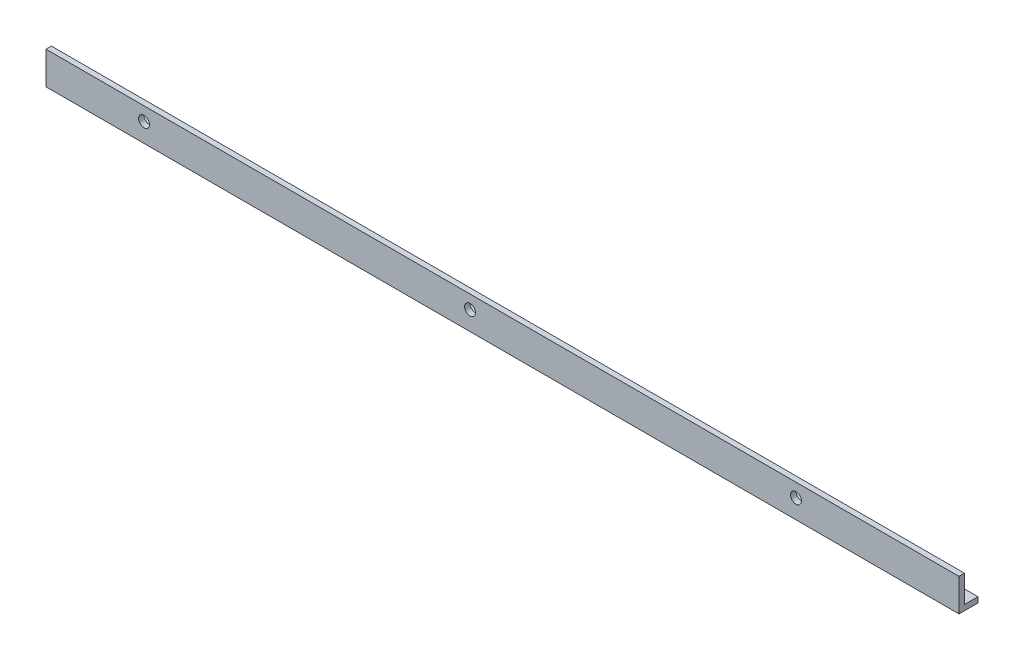
SolidWorks part; units mm, degrees
other "Markup1"
sketch "Sketch9" plane through (-9.88, -1.52, -2.5) normal (-1, 0, 0) x (0, 0, 1)
ref_plane "Alzado" through (0, 0, 0) normal (0, 0, 1) x (1, 0, 0)
ref_plane "Planta" through (0, 0, 0) normal (0, 1, 0) x (1, 0, 0)
ref_plane "Vista lateral" through (0, 0, 0) normal (1, 0, 0) x (0, 0, -1)
sketch "Sketch1" plane through (0, 0, 0) normal (0, 0, 1) x (1, 0, 0)
  line L1 (-14.6, 8.48) -> (50.12, 8.48)
  line L2 (-14.6, 8.48) -> (-14.6, -1.52)
  line L3 (-14.6, -1.52) -> (50.12, -1.52)
  line L4 (50.12, 8.48) -> (50.12, -1.52)
  dimension "D1" = 10
extrude "Boss-Extrude1" add sketch "Sketch1" along normal blind 1
sketch "Sketch2" plane through (0, 0, 0) normal (0, 0, -1) x (-1, 0, 0)
  line L0 (14.6, 8.48) -> (14.6, -1.52) construction
  line L1 (-50.12, -1.52) -> (14.6, -1.52)
  line L2 (-50.12, -1.52) -> (-50.12, -0.52)
  line L3 (-50.12, -0.52) -> (14.6, -0.52)
  line L4 (14.6, -1.52) -> (14.6, -0.52)
  dimension "D1" = 1
extrude "Boss-Extrude2" add sketch "Sketch2" along normal blind 5
sketch "Sketch3" plane through (50.12, 0, 0) normal (1, 0, 0) x (0, 0, -1)
  line L0 (-1, 8.48) -> (0, 8.48)
  line L1 (0, 8.48) -> (0, -0.52)
  line L2 (0, -0.52) -> (5, -0.52)
  line L3 (5, -0.52) -> (5, -1.52)
  line L4 (-1, -1.52) -> (5, -1.52) construction
  line L5 (5, -1.52) -> (-1, -1.52)
  line L6 (-1, -1.52) -> (-1, 8.48)
extrude "Boss-Extrude3" add sketch "Sketch3" along normal blind 60
sketch "Sketch4" plane through (110.12, 0, 0) normal (1, 0, 0) x (0, 0, -1)
  line L0 (0, -0.52) -> (0, 8.48) construction
  line L1 (-1, 8.48) -> (0, 8.48)
  line L2 (-1, 8.48) -> (-1, 3.48)
  line L3 (-1, 3.48) -> (0, 3.48)
  line L4 (0, 8.48) -> (0, 3.48)
  dimension "D1" = 5
extrude "Cut-Extrude1" cut sketch "Sketch4" against normal through all
sketch "Sketch5" plane through (0, 3.48, 0) normal (0, 1, 0) x (1, 0, 0)
  line L0 (110.12, -1) -> (-9.88, -1) construction
  line L1 (-14.6, -1) -> (110.12, -1) construction
  line L3 (-9.88, -1) -> (-14.6, -1)
  line L4 (-9.88, -1) -> (-9.88, 5)
  line L5 (-9.88, 5) -> (-14.6, 5)
  line L6 (-14.6, -1) -> (-14.6, 5)
  dimension "D1" = 120
extrude "Cut-Extrude2" cut sketch "Sketch5" against normal through all
sketch "Sketch6" plane through (0, 3.48, 0) normal (0, 1, 0) x (1, 0, 0)
  line L1 (-9.88, 0) -> (110.12, 0)
  line L2 (-9.88, 0) -> (-9.88, -1)
  line L3 (-9.88, -1) -> (110.12, -1)
  line L4 (110.12, 0) -> (110.12, -1)
extrude "Boss-Extrude4" add sketch "Sketch6" along normal blind 1
sketch "Sketch7" plane through (0, 0, 1) normal (0, 0, 1) x (1, 0, 0)
  line L0 (-9.88, -1.52) -> (-9.88, 4.48) construction
  line L1 (-9.88, 4.48) -> (110.12, 4.48) construction
  line L2 (110.12, 4.48) -> (110.12, -1.52) construction
  circle A0 centre (20.12, 1.98) radius 1
  circle A1 centre (80.12, 1.98) radius 1
  dimension "D1" = 30
  dimension "D3" = 30
  dimension "D2" = 2.5
extrude "Cut-Extrude3" cut sketch "Sketch7" against normal through all
sketch "Sketch8" plane through (0, -0.52, 0) normal (0, 1, 0) x (1, 0, 0)
  line L0 (110.12, 5) -> (110.12, 0) construction
  line L1 (-9.88, 5) -> (110.12, 5)
  line L2 (-9.88, 5) -> (-9.88, 2.5)
  line L3 (-9.88, 2.5) -> (110.12, 2.5)
  line L4 (110.12, 5) -> (110.12, 2.5)
extrude "Cut-Extrude4" cut sketch "Sketch8" against normal through all
sketch "Sketch11" plane through (-9.88, 0, 0) normal (-1, 0, 0) x (0, 0, 1)
  line L0 (-2.5, -0.52) -> (-2.5, -1.52)
  line L1 (-2.5, -1.52) -> (1, -1.52)
  line L2 (1, -1.52) -> (1, 4.48)
  line L3 (1, 4.48) -> (0, 4.48)
  line L4 (0, 4.48) -> (0, -0.52)
  line L5 (0, -0.52) -> (-2.5, -0.52)
extrude "Boss-Extrude5" add sketch "Sketch11" along normal blind 48.05
sketch "Sketch13" plane through (0, 0, 0) normal (0, 0, -1) x (-1, 0, 0)
  line L0 (-20.12, 1.98) -> (39.88, 1.98) construction
  circle A0 centre (39.88, 1.98) radius 1
  dimension "D1" = 60
extrude "Cut-Extrude5" cut sketch "Sketch13" against normal through all
